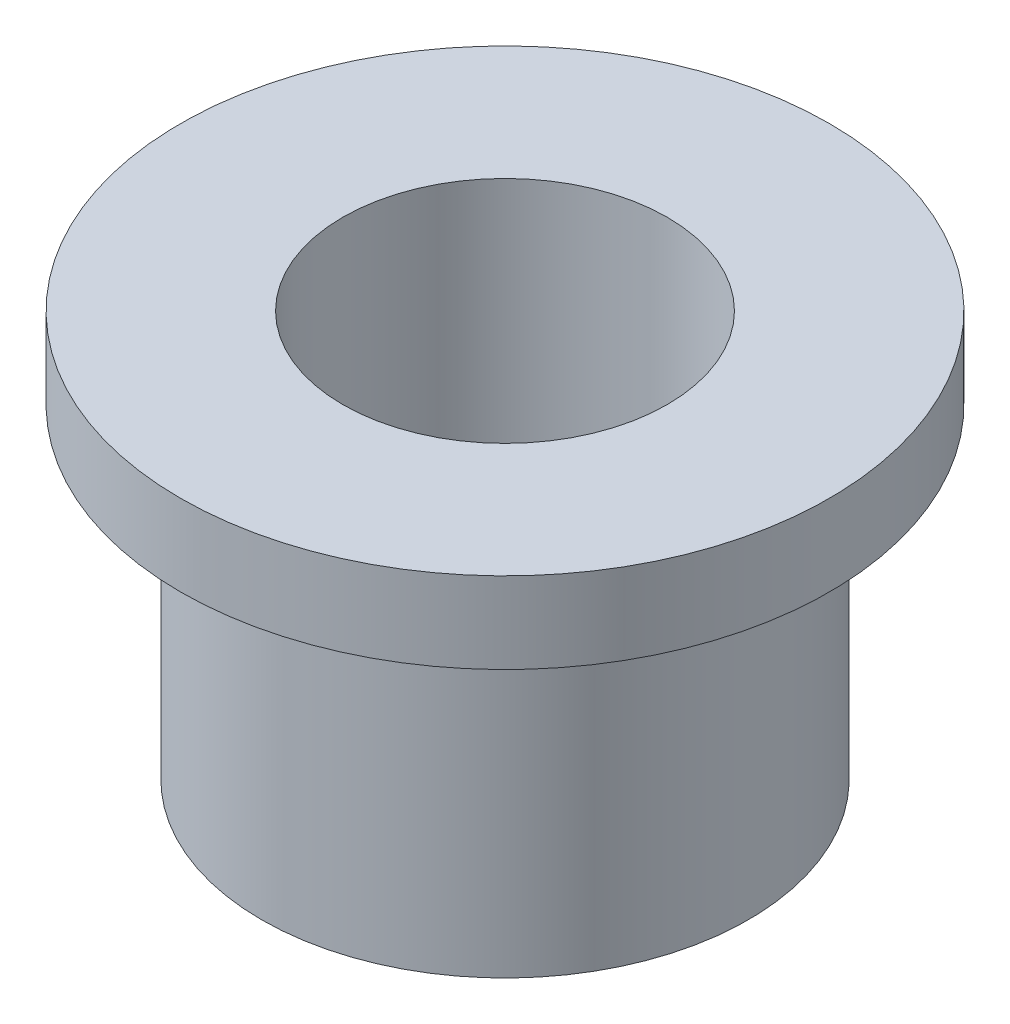
SolidWorks part; units mm, degrees
material "Aluminum Bronze"
ref_plane "Front Plane" through (0, 0, 0) normal (0, 0, 1) x (1, 0, 0)
ref_plane "Top Plane" through (0, 0, 0) normal (0, 1, 0) x (1, 0, 0)
ref_plane "Right Plane" through (0, 0, 0) normal (1, 0, 0) x (0, 0, -1)
sketch "Sketch1" plane through (0, 0, 0) normal (0, 1, 0) x (1, 0, 0)
  circle A0 centre (0, 0) radius 4.7625
  circle A1 centre (0, 0) radius 3.175
  dimension "D1" = 6.35
  dimension "D2" = 9.525
extrude "Boss-Extrude1" add sketch "Sketch1" along normal blind 6.35
sketch "Sketch2" plane through (0, 6.35, 0) normal (0, 1, 0) x (1, 0, 0)
  circle A0 centre (0, 0) radius 3.175 construction
  circle A1 centre (0, 0) radius 3.175
  circle A2 centre (0, 0) radius 6.35
  dimension "D1" = 12.7
extrude "Boss-Extrude2" add sketch "Sketch2" along normal blind 1.5875
